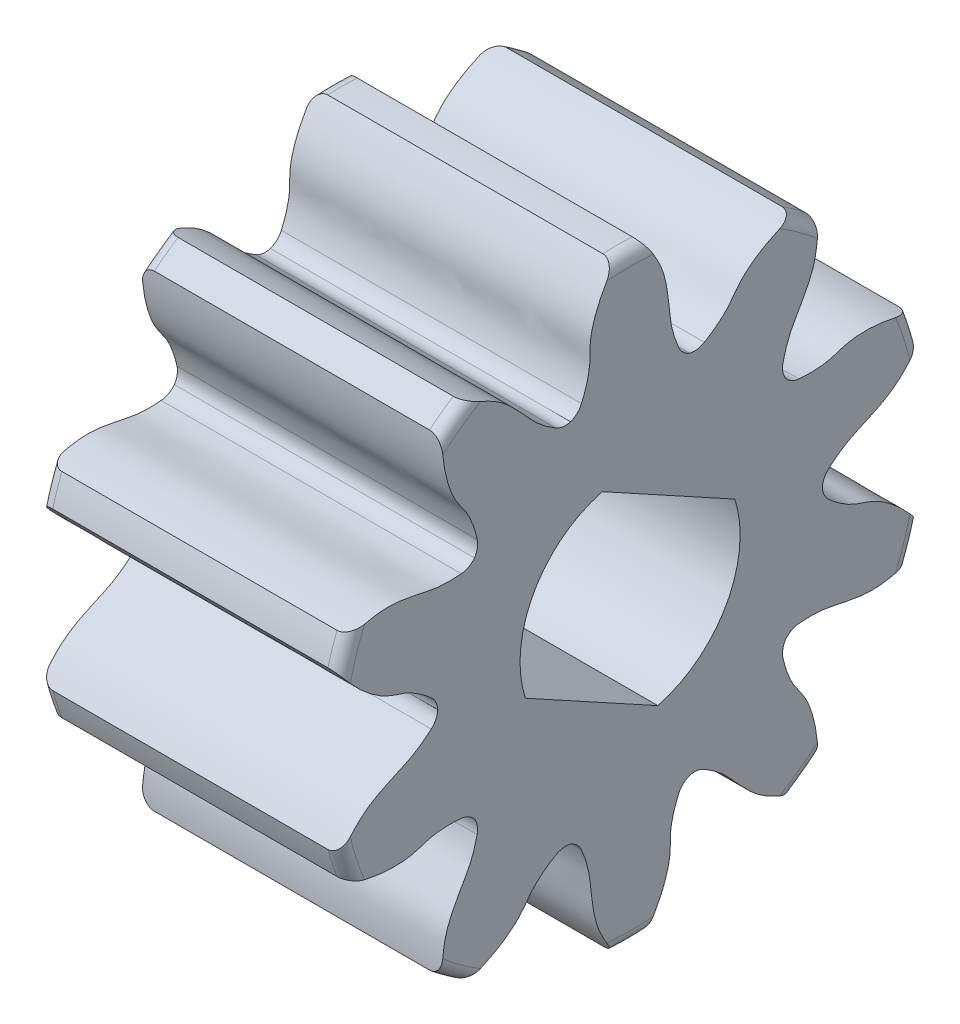
SolidWorks part; units mm, degrees
material "ABS"
ref_plane "Front Plane" through (0, 0, 0) normal (0, 0, 1) x (1, 0, 0)
ref_plane "Top Plane" through (0, 0, 0) normal (0, 1, 0) x (1, 0, 0)
ref_plane "Right Plane" through (0, 0, 0) normal (1, 0, 0) x (0, 0, -1)
sketch "Sketch1" plane through (0, 0, 0) normal (0, 0, 1) x (1, 0, 0)
  line L0 (-2, 2.4) -> (-2, 0)
  line L1 (-2, 0) -> (0.4, 0)
  line L2 (0.4, 0) -> (0.4, 2.4)
  line L3 (0.4, 2.4) -> (-2, 2.4)
  line L4 (-2, 0) -> (0.4, 0) construction
  dimension "D1" = 2.4
revolve "Revolve1" add sketch "Sketch1" angle 360 about L4
sketch "Sketch2" plane through (-2, 0, 0) normal (-1, 0, 0) x (0, 0, 1)
  arc A0 (1.3139, 2.0084) -> (0.1175, 2.3971) centre (0, 0) ccw
  arc A1 (0.3886, 1.5452) -> (0.4751, 1.4622) centre (0.5316, 1.6076) ccw
  arc A2 (0.4751, 1.4622) -> (0.5939, 1.4785) centre (0.5149, 1.613) ccw
  spline S0 degree 3 poles (0.1175, 2.3971) (0.1418, 2.3633) (0.1647, 2.3284) (0.1858, 2.2925) (0.2401, 2.2006) (0.2851, 2.1009) (0.3083, 1.9968) (0.3199, 1.9447) (0.3229, 1.8906) (0.3211, 1.8373) (0.3193, 1.7838) (0.3283, 1.7298) (0.3418, 1.678) (0.3537, 1.6326) (0.3698, 1.5882) (0.3886, 1.5452) knots -0.000124 -0.000124 -0.000124 -0.000124 0 0 0 0.00032 0.00032 0.00032 0.000479 0.000479 0.000479 0.00064 0.00064 0.00064 0.00078 0.00078 0.00078 0.00078
  spline S1 degree 3 poles (0.5939, 1.4785) (0.6608, 1.5178) (0.7244, 1.5647) (0.7778, 1.621) (0.8768, 1.7255) (0.9686, 1.8452) (1.095, 1.9141) (1.1283, 1.9322) (1.1624, 1.9488) (1.1971, 1.9639) (1.2354, 1.9805) (1.2744, 1.9953) (1.3139, 2.0084) knots 0 0 0 0 0.000233 0.000233 0.000233 0.00066 0.00066 0.00066 0.00077 0.00077 0.00077 0.00089 0.00089 0.00089 0.00089
extrude "Cut-Extrude1" cut sketch "Sketch2" against normal through all
sketch "Sketch3" plane through (-2, 0, 0) normal (-1, 0, 0) x (0, 0, 1)
  arc A0 (2.2435, 0.8525) -> (1.504, 1.8703) centre (0, 0) ccw
  arc A1 (1.2226, 1.0217) -> (1.2438, 0.9037) centre (1.375, 0.9881) ccw
  arc A2 (1.2438, 0.9037) -> (1.3495, 0.8471) centre (1.3647, 1.0023) ccw
  spline S0 degree 3 poles (1.504, 1.8703) (1.5038, 1.8286) (1.5018, 1.7869) (1.4978, 1.7454) (1.4877, 1.6392) (1.4656, 1.5321) (1.4231, 1.4342) (1.4019, 1.3853) (1.3725, 1.3397) (1.3397, 1.2977) (1.3068, 1.2554) (1.2824, 1.2065) (1.2629, 1.1566) (1.2458, 1.1129) (1.2327, 1.0675) (1.2226, 1.0217) knots -0.000124 -0.000124 -0.000124 -0.000124 0 0 0 0.00032 0.00032 0.00032 0.000479 0.000479 0.000479 0.00064 0.00064 0.00064 0.00078 0.00078 0.00078 0.00078
  spline S1 degree 3 poles (1.3495, 0.8471) (1.4267, 0.8395) (1.5058, 0.8401) (1.582, 0.8543) (1.7236, 0.8806) (1.8682, 0.9234) (2.011, 0.9049) (2.0485, 0.9) (2.0859, 0.8934) (2.1228, 0.8852) (2.1635, 0.8761) (2.2038, 0.8651) (2.2435, 0.8525) knots 0 0 0 0 0.000233 0.000233 0.000233 0.00066 0.00066 0.00066 0.00077 0.00077 0.00077 0.00089 0.00089 0.00089 0.00089
extrude "Cut-Extrude2" cut sketch "Sketch3" against normal through all
sketch "Sketch4" plane through (-2, 0, 0) normal (-1, 0, 0) x (0, 0, 1)
  arc A0 (2.3161, -0.629) -> (2.3161, 0.629) centre (0, 0) ccw
  arc A1 (1.5897, 0.1079) -> (1.5374, 0) centre (1.6932, -0.0088) ccw
  arc A2 (1.5374, 0) -> (1.5897, -0.1079) centre (1.6932, 0.0088) ccw
  spline S0 degree 3 poles (2.3161, 0.629) (2.2914, 0.5955) (2.2653, 0.5629) (2.2377, 0.5317) (2.1671, 0.4517) (2.0862, 0.378) (1.9943, 0.3238) (1.9484, 0.2967) (1.8978, 0.2771) (1.8466, 0.2624) (1.7951, 0.2476) (1.7466, 0.2223) (1.7015, 0.1934) (1.662, 0.1681) (1.6248, 0.1391) (1.5897, 0.1079) knots -0.000124 -0.000124 -0.000124 -0.000124 0 0 0 0.00032 0.00032 0.00032 0.000479 0.000479 0.000479 0.00064 0.00064 0.00064 0.00078 0.00078 0.00078 0.00078
  spline S1 degree 3 poles (1.5897, -0.1079) (1.6477, -0.1594) (1.712, -0.2054) (1.782, -0.2388) (1.912, -0.3006) (2.0542, -0.351) (2.1588, -0.45) (2.1863, -0.476) (2.2126, -0.5033) (2.2377, -0.5317) (2.2653, -0.5629) (2.2914, -0.5955) (2.3161, -0.629) knots 0 0 0 0 0.000233 0.000233 0.000233 0.00066 0.00066 0.00066 0.00077 0.00077 0.00077 0.00089 0.00089 0.00089 0.00089
extrude "Cut-Extrude3" cut sketch "Sketch4" against normal through all
sketch "Sketch5" plane through (-2, 0, 0) normal (-1, 0, 0) x (0, 0, 1)
  arc A0 (1.504, -1.8703) -> (2.2435, -0.8525) centre (0, 0) ccw
  arc A1 (1.3495, -0.8471) -> (1.2438, -0.9037) centre (1.3647, -1.0023) ccw
  arc A2 (1.2438, -0.9037) -> (1.2226, -1.0217) centre (1.375, -0.9881) ccw
  spline S0 degree 3 poles (2.2435, -0.8525) (2.2038, -0.8651) (2.1635, -0.8761) (2.1228, -0.8852) (2.0187, -0.9084) (1.91, -0.9204) (1.8038, -0.9102) (1.7507, -0.9052) (1.6983, -0.8913) (1.6481, -0.8731) (1.5978, -0.8549) (1.5437, -0.8468) (1.4903, -0.8436) (1.4434, -0.8409) (1.3962, -0.8425) (1.3495, -0.8471) knots -0.000124 -0.000124 -0.000124 -0.000124 0 0 0 0.00032 0.00032 0.00032 0.000479 0.000479 0.000479 0.00064 0.00064 0.00064 0.00078 0.00078 0.00078 0.00078
  spline S1 degree 3 poles (1.2226, -1.0217) (1.2393, -1.0974) (1.2643, -1.1725) (1.3013, -1.2406) (1.3701, -1.3671) (1.4555, -1.4914) (1.482, -1.6329) (1.489, -1.6701) (1.4942, -1.7077) (1.4978, -1.7454) (1.5018, -1.7869) (1.5038, -1.8286) (1.504, -1.8703) knots 0 0 0 0 0.000233 0.000233 0.000233 0.00066 0.00066 0.00066 0.00077 0.00077 0.00077 0.00089 0.00089 0.00089 0.00089
extrude "Cut-Extrude4" cut sketch "Sketch5" against normal through all
sketch "Sketch6" plane through (-2, 0, 0) normal (-1, 0, 0) x (0, 0, 1)
  arc A0 (0.1175, -2.3971) -> (1.3139, -2.0084) centre (0, 0) ccw
  arc A1 (0.5939, -1.4785) -> (0.4751, -1.4622) centre (0.5149, -1.613) ccw
  arc A2 (0.4751, -1.4622) -> (0.3886, -1.5452) centre (0.5316, -1.6076) ccw
  spline S0 degree 3 poles (1.3139, -2.0084) (1.2744, -1.9953) (1.2354, -1.9805) (1.1971, -1.9639) (1.0993, -1.9214) (1.0042, -1.8673) (0.9242, -1.7966) (0.8843, -1.7613) (0.85, -1.7193) (0.8202, -1.6751) (0.7902, -1.6308) (0.7511, -1.5925) (0.7098, -1.5585) (0.6735, -1.5287) (0.6344, -1.5023) (0.5939, -1.4785) knots -0.000124 -0.000124 -0.000124 -0.000124 0 0 0 0.00032 0.00032 0.00032 0.000479 0.000479 0.000479 0.00064 0.00064 0.00064 0.00078 0.00078 0.00078 0.00078
  spline S1 degree 3 poles (0.3886, -1.5452) (0.3576, -1.6163) (0.3336, -1.6917) (0.3236, -1.7686) (0.3049, -1.9113) (0.3009, -2.0621) (0.2392, -2.1922) (0.2229, -2.2264) (0.2051, -2.2599) (0.1858, -2.2925) (0.1647, -2.3284) (0.1418, -2.3633) (0.1175, -2.3971) knots 0 0 0 0 0.000233 0.000233 0.000233 0.00066 0.00066 0.00066 0.00077 0.00077 0.00077 0.00089 0.00089 0.00089 0.00089
extrude "Cut-Extrude5" cut sketch "Sketch6" against normal through all
sketch "Sketch7" plane through (-2, 0, 0) normal (-1, 0, 0) x (0, 0, 1)
  arc A0 (-1.3139, -2.0084) -> (-0.1175, -2.3971) centre (0, 0) ccw
  arc A1 (-0.3886, -1.5452) -> (-0.4751, -1.4622) centre (-0.5316, -1.6076) ccw
  arc A2 (-0.4751, -1.4622) -> (-0.5939, -1.4785) centre (-0.5149, -1.613) ccw
  spline S0 degree 3 poles (-0.1175, -2.3971) (-0.1418, -2.3633) (-0.1647, -2.3284) (-0.1858, -2.2925) (-0.2401, -2.2006) (-0.2851, -2.1009) (-0.3083, -1.9968) (-0.3199, -1.9447) (-0.3229, -1.8906) (-0.3211, -1.8373) (-0.3193, -1.7838) (-0.3283, -1.7298) (-0.3418, -1.678) (-0.3537, -1.6326) (-0.3698, -1.5882) (-0.3886, -1.5452) knots -0.000124 -0.000124 -0.000124 -0.000124 0 0 0 0.00032 0.00032 0.00032 0.000479 0.000479 0.000479 0.00064 0.00064 0.00064 0.00078 0.00078 0.00078 0.00078
  spline S1 degree 3 poles (-0.5939, -1.4785) (-0.6608, -1.5178) (-0.7244, -1.5647) (-0.7778, -1.621) (-0.8768, -1.7255) (-0.9686, -1.8452) (-1.095, -1.9141) (-1.1283, -1.9322) (-1.1624, -1.9488) (-1.1971, -1.9639) (-1.2354, -1.9805) (-1.2744, -1.9953) (-1.3139, -2.0084) knots 0 0 0 0 0.000233 0.000233 0.000233 0.00066 0.00066 0.00066 0.00077 0.00077 0.00077 0.00089 0.00089 0.00089 0.00089
extrude "Cut-Extrude6" cut sketch "Sketch7" against normal through all
sketch "Sketch8" plane through (-2, 0, 0) normal (-1, 0, 0) x (0, 0, 1)
  arc A0 (-2.2435, -0.8525) -> (-1.504, -1.8703) centre (0, 0) ccw
  arc A1 (-1.2226, -1.0217) -> (-1.2438, -0.9037) centre (-1.375, -0.9881) ccw
  arc A2 (-1.2438, -0.9037) -> (-1.3495, -0.8471) centre (-1.3647, -1.0023) ccw
  spline S0 degree 3 poles (-1.504, -1.8703) (-1.5038, -1.8286) (-1.5018, -1.7869) (-1.4978, -1.7454) (-1.4877, -1.6392) (-1.4656, -1.5321) (-1.4231, -1.4342) (-1.4019, -1.3853) (-1.3725, -1.3397) (-1.3397, -1.2977) (-1.3068, -1.2554) (-1.2824, -1.2065) (-1.2629, -1.1566) (-1.2458, -1.1129) (-1.2327, -1.0675) (-1.2226, -1.0217) knots -0.000124 -0.000124 -0.000124 -0.000124 0 0 0 0.00032 0.00032 0.00032 0.000479 0.000479 0.000479 0.00064 0.00064 0.00064 0.00078 0.00078 0.00078 0.00078
  spline S1 degree 3 poles (-1.3495, -0.8471) (-1.4267, -0.8395) (-1.5058, -0.8401) (-1.582, -0.8543) (-1.7236, -0.8806) (-1.8682, -0.9234) (-2.011, -0.9049) (-2.0485, -0.9) (-2.0859, -0.8934) (-2.1228, -0.8852) (-2.1635, -0.8761) (-2.2038, -0.8651) (-2.2435, -0.8525) knots 0 0 0 0 0.000233 0.000233 0.000233 0.00066 0.00066 0.00066 0.00077 0.00077 0.00077 0.00089 0.00089 0.00089 0.00089
extrude "Cut-Extrude7" cut sketch "Sketch8" against normal through all
sketch "Sketch9" plane through (-2, 0, 0) normal (-1, 0, 0) x (0, 0, 1)
  arc A0 (-2.3161, 0.629) -> (-2.3161, -0.629) centre (0, 0) ccw
  arc A1 (-1.5897, -0.1079) -> (-1.5374, 0) centre (-1.6932, 0.0088) ccw
  arc A2 (-1.5374, 0) -> (-1.5897, 0.1079) centre (-1.6932, -0.0088) ccw
  spline S0 degree 3 poles (-2.3161, -0.629) (-2.2914, -0.5955) (-2.2653, -0.5629) (-2.2377, -0.5317) (-2.1671, -0.4517) (-2.0862, -0.378) (-1.9943, -0.3238) (-1.9484, -0.2967) (-1.8978, -0.2771) (-1.8466, -0.2624) (-1.7951, -0.2476) (-1.7466, -0.2223) (-1.7015, -0.1934) (-1.662, -0.1681) (-1.6248, -0.1391) (-1.5897, -0.1079) knots -0.000124 -0.000124 -0.000124 -0.000124 0 0 0 0.00032 0.00032 0.00032 0.000479 0.000479 0.000479 0.00064 0.00064 0.00064 0.00078 0.00078 0.00078 0.00078
  spline S1 degree 3 poles (-1.5897, 0.1079) (-1.6477, 0.1594) (-1.712, 0.2054) (-1.782, 0.2388) (-1.912, 0.3006) (-2.0542, 0.351) (-2.1588, 0.45) (-2.1863, 0.476) (-2.2126, 0.5033) (-2.2377, 0.5317) (-2.2653, 0.5629) (-2.2914, 0.5955) (-2.3161, 0.629) knots 0 0 0 0 0.000233 0.000233 0.000233 0.00066 0.00066 0.00066 0.00077 0.00077 0.00077 0.00089 0.00089 0.00089 0.00089
extrude "Cut-Extrude8" cut sketch "Sketch9" against normal through all
sketch "Sketch10" plane through (-2, 0, 0) normal (-1, 0, 0) x (0, 0, 1)
  arc A0 (-1.504, 1.8703) -> (-2.2435, 0.8525) centre (0, 0) ccw
  arc A1 (-1.3495, 0.8471) -> (-1.2438, 0.9037) centre (-1.3647, 1.0023) ccw
  arc A2 (-1.2438, 0.9037) -> (-1.2226, 1.0217) centre (-1.375, 0.9881) ccw
  spline S0 degree 3 poles (-2.2435, 0.8525) (-2.2038, 0.8651) (-2.1635, 0.8761) (-2.1228, 0.8852) (-2.0187, 0.9084) (-1.91, 0.9204) (-1.8038, 0.9102) (-1.7507, 0.9052) (-1.6983, 0.8913) (-1.6481, 0.8731) (-1.5978, 0.8549) (-1.5437, 0.8468) (-1.4903, 0.8436) (-1.4434, 0.8409) (-1.3962, 0.8425) (-1.3495, 0.8471) knots -0.000124 -0.000124 -0.000124 -0.000124 0 0 0 0.00032 0.00032 0.00032 0.000479 0.000479 0.000479 0.00064 0.00064 0.00064 0.00078 0.00078 0.00078 0.00078
  spline S1 degree 3 poles (-1.2226, 1.0217) (-1.2393, 1.0974) (-1.2643, 1.1725) (-1.3013, 1.2406) (-1.3701, 1.3671) (-1.4555, 1.4914) (-1.482, 1.6329) (-1.489, 1.6701) (-1.4942, 1.7077) (-1.4978, 1.7454) (-1.5018, 1.7869) (-1.5038, 1.8286) (-1.504, 1.8703) knots 0 0 0 0 0.000233 0.000233 0.000233 0.00066 0.00066 0.00066 0.00077 0.00077 0.00077 0.00089 0.00089 0.00089 0.00089
extrude "Cut-Extrude9" cut sketch "Sketch10" against normal through all
sketch "Sketch11" plane through (-2, 0, 0) normal (-1, 0, 0) x (0, 0, 1)
  arc A0 (-0.1175, 2.3971) -> (-1.3139, 2.0084) centre (0, 0) ccw
  arc A1 (-0.5939, 1.4785) -> (-0.4751, 1.4622) centre (-0.5149, 1.613) ccw
  arc A2 (-0.4751, 1.4622) -> (-0.3886, 1.5452) centre (-0.5316, 1.6076) ccw
  spline S0 degree 3 poles (-1.3139, 2.0084) (-1.2744, 1.9953) (-1.2354, 1.9805) (-1.1971, 1.9639) (-1.0993, 1.9214) (-1.0042, 1.8673) (-0.9242, 1.7966) (-0.8843, 1.7613) (-0.85, 1.7193) (-0.8202, 1.6751) (-0.7902, 1.6308) (-0.7511, 1.5925) (-0.7098, 1.5585) (-0.6735, 1.5287) (-0.6344, 1.5023) (-0.5939, 1.4785) knots -0.000124 -0.000124 -0.000124 -0.000124 0 0 0 0.00032 0.00032 0.00032 0.000479 0.000479 0.000479 0.00064 0.00064 0.00064 0.00078 0.00078 0.00078 0.00078
  spline S1 degree 3 poles (-0.3886, 1.5452) (-0.3576, 1.6163) (-0.3336, 1.6917) (-0.3236, 1.7686) (-0.3049, 1.9113) (-0.3009, 2.0621) (-0.2392, 2.1922) (-0.2229, 2.2264) (-0.2051, 2.2599) (-0.1858, 2.2925) (-0.1647, 2.3284) (-0.1418, 2.3633) (-0.1175, 2.3971) knots 0 0 0 0 0.000233 0.000233 0.000233 0.00066 0.00066 0.00066 0.00077 0.00077 0.00077 0.00089 0.00089 0.00089 0.00089
extrude "Cut-Extrude10" cut sketch "Sketch11" against normal through all
fillet "Fillet1" radius 0.1 20 edges at (-2, 1.9416, 1.4107) (0.4, -1.9416, 1.4107) (-2, 1.9416, -1.4107) (0.4, 0.7416, -2.2825) (-2, -2.4, 0) (0.4, 0.7416, 2.2825) (0.4, -1.9416, -1.4107) (0.4, 2.4, 0) (-2, -0.7416, 2.2825) (-2, -0.7416, -2.2825) (0.4, 1.9416, 1.4107) (0.4, -0.7416, 2.2825) (0.4, -2.4, 0) (0.4, -0.7416, -2.2825) (0.4, 1.9416, -1.4107) (-2, 2.4, 0) (-2, 0.7416, 2.2825) (-2, -1.9416, 1.4107) (-2, -1.9416, -1.4107) (-2, 0.7416, -2.2825)
scale "Scale1" scale about centroid uniform scaling yes scale factor 2.5
sketch "Sketch14" plane through (2.2, 0, 0) normal (1, 0, 0) x (0, 0, -1)
  line L0 (-2.0933, -0.6767) -> (0.5545, -2.129)
  line L1 (-2.0933, -0.6767) -> (-0.5545, 2.129)
  line L2 (0.5545, -2.129) -> (2.0933, 0.6767)
  line L3 (-0.5545, 2.129) -> (2.0933, 0.6767)
  line L4 (-2.0933, -0.6767) -> (2.0933, 0.6767) construction
  line L5 (0.5545, -2.129) -> (-0.5545, 2.129) construction
  arc A0 (-0.5545, 2.129) -> (-2.0933, -0.6767) centre (0, 0) ccw
  arc A1 (2.0933, 0.6767) -> (0.5545, -2.129) centre (0, 0) cw
  point P1 (0, 0)
  point P11 (-1.9289, 1.0579)
  point P12 (1.9289, -1.0579)
  dimension "D1" = 4.4
  dimension "D2" = 3.2
extrude "Cut-Extrude11" cut sketch "Sketch14" against normal up to surface (6 mm away) contours L3 L1 L0 L2 | L1 A0 | A1 L2
